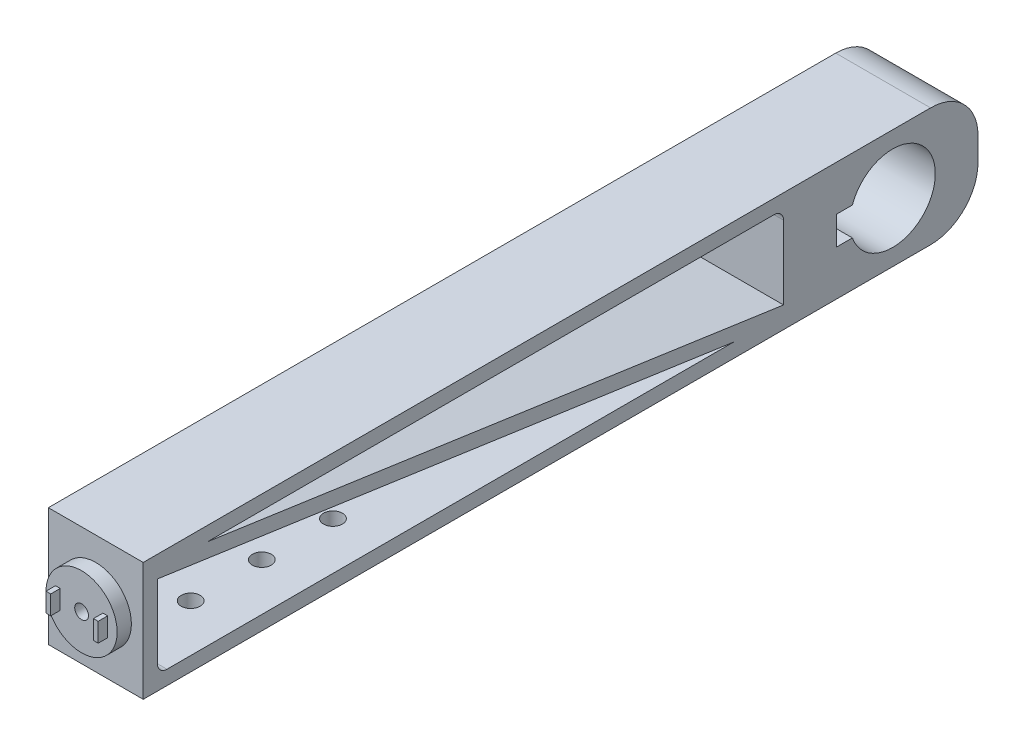
SolidWorks part; units mm, degrees
material "Alloy Steel (SS)"
ref_plane "Front Plane" through (0, 0, 0) normal (0, 0, 1) x (1, 0, 0)
ref_plane "Top Plane" through (0, 0, 0) normal (0, 1, 0) x (1, 0, 0)
ref_plane "Right Plane" through (0, 0, 0) normal (1, 0, 0) x (0, 0, -1)
sketch "Sketch2" plane through (0, 0, 0) normal (1, 0, 0) x (0, 0, -1)
  line L0 (-85, -9.5) -> (47, -9.5)
  line L1 (-88, 12.5) -> (78, 12.5)
  line L2 (-88, 12.5) -> (-88, 9.5)
  line L3 (-88, -12.5) -> (78, -12.5)
  line L4 (88, 2.5) -> (88, -2.5)
  line L5 (-88, 12.5) -> (88, -12.5) construction
  line L6 (-88, -12.5) -> (88, 12.5) construction
  line L7 (-85, 9.5) -> (47, 9.5)
  line L8 (47, 9.5) -> (47, -9.5)
  line L9 (-88, -9.5) -> (-88, -12.5)
  line L10 (-88, 9.5) -> (78, 9.5) construction
  line L11 (-88, -9.5) -> (78, -9.5) construction
  line L12 (-88, 9.5) -> (-88, -9.5)
  line L13 (-85, 9.5) -> (-85, -9.5)
  line L14 (-85, 9.5) -> (47, -9.5) construction
  line L15 (-85, 7.9845) -> (36.4715, -9.5)
  line L16 (-74.4715, 9.5) -> (47, -7.9845)
  line L17 (-84.7863, 10.9847) -> (47.2137, -8.0153) construction
  line L18 (-85.2137, 8.0153) -> (46.7863, -10.9847) construction
  line L19 (70, 0) -> (58.2, 0) construction
  line L20 (61.5147, 3) -> (58.2, 3)
  line L21 (61.5147, -3) -> (58.2, -3)
  line L22 (58.2, 3) -> (58.2, -3)
  line L23 (70, 3) -> (58.2, 3) construction
  line L24 (70, -3) -> (58.2, -3) construction
  arc A0 (78, -12.5) -> (88, -2.5) centre (78, -2.5) ccw
  arc A1 (88, 2.5) -> (78, 12.5) centre (78, 2.5) ccw
  arc A2 (61.5147, -3) -> (61.5147, 3) centre (70, 0) ccw
  point P0 (0, 0)
  dimension "D3" = 10
  dimension "D4" = 18
  dimension "D1" = 25
  dimension "D2" = 176
  dimension "D5" = 18
  dimension "D6" = 9.5
  dimension "D7" = 9.5
  dimension "D8" = 23
  dimension "D9" = 3
  dimension "D12" = 11.8
  dimension "D10" = 1.5
  dimension "D11" = 1.5
  dimension "D13" = 3
  dimension "D14" = 3
extrude "Boss-Extrude1" add sketch "Sketch2" along normal blind 20 contours L4 A1 L1 L2 L12 L9 L3 A0 A2 L21 L22 L20 L13 L7 L8 L0 | L16 L7 L13 L15 L0 L8
sketch "Sketch3" plane through (0, 0, 88) normal (0, 0, 1) x (1, 0, 0)
  line L0 (10, 12.5) -> (10, -12.5) construction
  line L1 (20, 12.5) -> (0, 12.5) construction
  line L2 (20, -12.5) -> (0, -12.5) construction
  circle A0 centre (10, 0) radius 7.5
  dimension "D1" = 15
extrude "Boss-Extrude2" add sketch "Sketch3" along normal blind 3
sketch "Sketch4" plane through (0, 0, 91) normal (0, 0, 1) x (1, 0, 0)
  line L0 (0, 0) -> (20, 0) construction
  line L1 (20, 12.5) -> (20, -12.5) construction
  line L2 (10, 12.5) -> (10, -12.5) construction
  line L3 (20, 12.5) -> (0, 12.5) construction
  line L4 (20, -12.5) -> (0, -12.5) construction
  line L5 (4.5, -2) -> (5.5, -2)
  line L6 (15.5, -2) -> (14.5, -2)
  line L7 (15.5, -2) -> (15.5, 2)
  line L8 (15.5, 2) -> (14.5, 2)
  line L9 (14.5, -2) -> (14.5, 2)
  line L10 (15.5, -2) -> (14.5, 2) construction
  line L11 (15.5, 2) -> (14.5, -2) construction
  line L12 (4.5, -2) -> (4.5, 2)
  line L13 (4.5, 2) -> (5.5, 2)
  line L14 (5.5, -2) -> (5.5, 2)
  point P11 (15, 0)
  dimension "D1" = 4.5
  dimension "D2" = 1
  dimension "D3" = 4
extrude "Boss-Extrude3" add sketch "Sketch4" along normal blind 2
sketch "Sketch5" plane through (0, 0, 91) normal (0, 0, 1) x (1, 0, 0)
  circle A0 centre (10, 0) radius 1.45
  dimension "D1" = 2.9
extrude "Cut-Extrude1" cut sketch "Sketch5" against normal up to next
fillet "Fillet1" radius 2 2 edges at (10, -9.5, 85) (10, 9.5, -47)
ref_plane "Plane1" through (10, 0, 0) normal (1, 0, 0) x (0, 0, -1)
sketch "Sketch6" plane through (0, -9.5, 0) normal (0, 1, 0) x (1, 0, 0)
  line L0 (10, 70) -> (10, -195.2021) construction
  circle A0 centre (10, -53) radius 2
  circle A1 centre (10, -68) radius 2
  circle A2 centre (10, -38) radius 2
  dimension "D2" = 4
  dimension "D3" = 4
  dimension "D5" = 15
  dimension "D1" = 35
  dimension "D4" = 15
extrude "Cut-Extrude2" cut sketch "Sketch6" against normal blind 10
